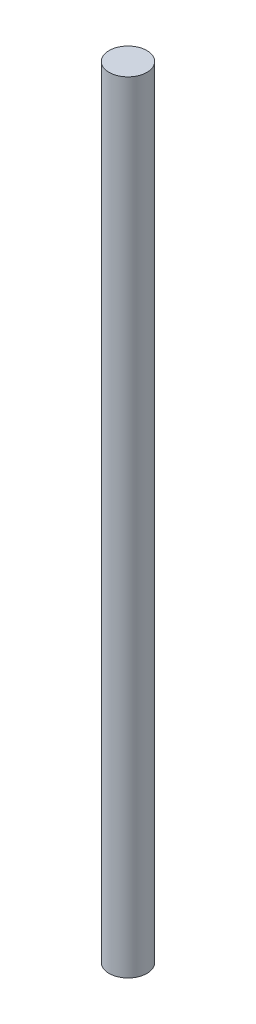
SolidWorks part; units mm, degrees
ref_plane "Front Plane" through (0, 0, 0) normal (0, 0, 1) x (1, 0, 0)
ref_plane "Top Plane" through (0, 0, 0) normal (0, 1, 0) x (1, 0, 0)
ref_plane "Right Plane" through (0, 0, 0) normal (1, 0, 0) x (0, 0, -1)
ref_plane "Plane1" through (0, 131, 0) normal (0, 1, 0) x (1, 0, 0)
sketch "Sketch1" plane through (0, 0, 0) normal (0, 1, 0) x (1, 0, 0)
  circle A0 centre (0, 0) radius 6.35
extrude "Boss-Extrude1" add sketch "Sketch1" along normal blind 262 contours A0
sketch "Sketch2" plane through (0, 131, 0) normal (0, 1, 0) x (1, 0, 0)
  line L1 (-1.5875, 7.7486) -> (1.5875, 7.7486)
  line L2 (-1.5875, 7.7486) -> (-1.5875, 4.5482)
  line L3 (-1.5875, 4.5482) -> (1.5875, 4.5482)
  line L4 (1.5875, 7.7486) -> (1.5875, 4.5482)
extrude "Cut-Extrude1" cut sketch "Sketch2" along normal blind 12.7 and the other way blind 12.7
